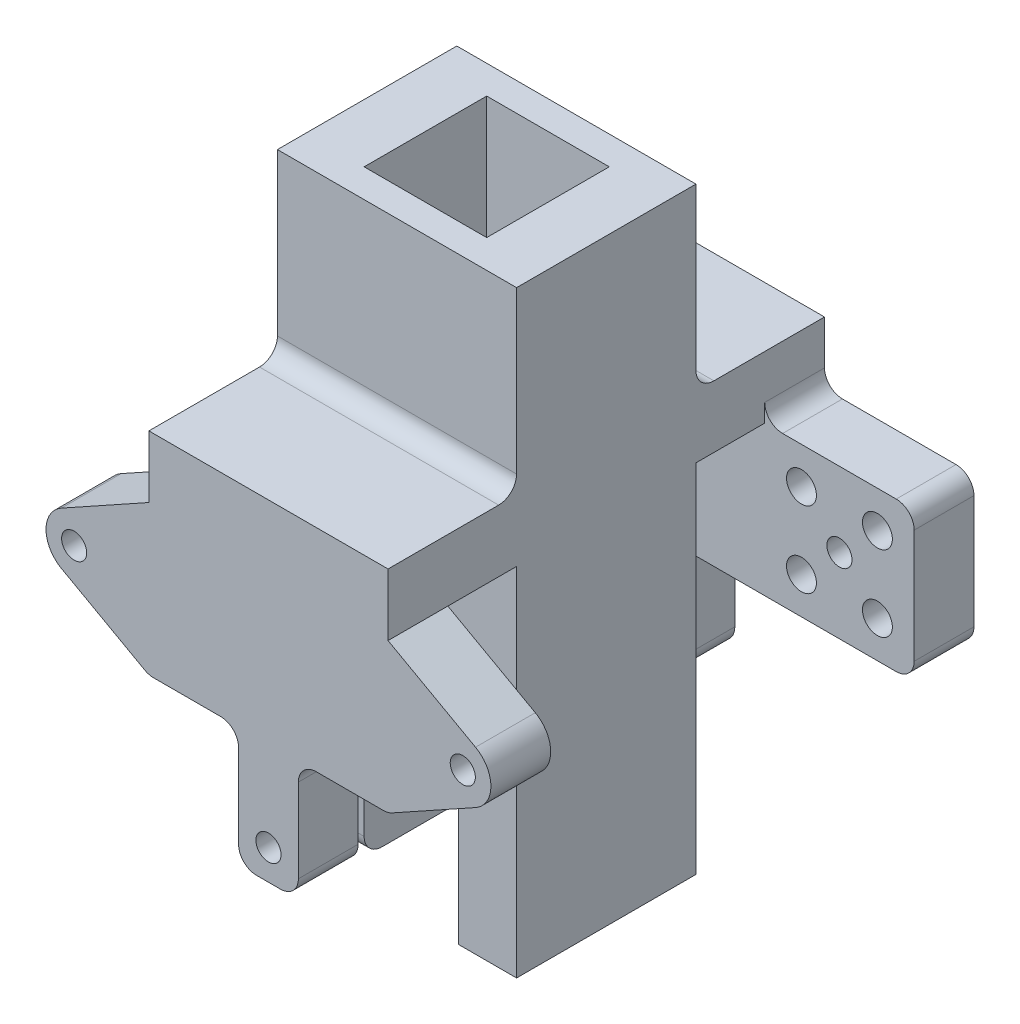
SolidWorks part; units mm, degrees
ref_plane "Front Plane" through (0, 0, 0) normal (0, 0, 1) x (1, 0, 0)
ref_plane "Top Plane" through (0, 0, 0) normal (0, 1, 0) x (1, 0, 0)
ref_plane "Right Plane" through (0, 0, 0) normal (1, 0, 0) x (0, 0, -1)
sketch "Sketch2" plane through (0, 0, 0) normal (0, 1, 0) x (1, 0, 0)
  line L14 (-20, 15) -> (20, 15)
  line L15 (-20, 15) -> (-20, -15)
  line L16 (-20, -15) -> (20, -15)
  line L17 (20, 15) -> (20, -15)
  line L18 (-20, 15) -> (20, -15) construction
  line L19 (-20, -15) -> (20, 15) construction
  point P0 (0, 0)
  dimension "D1" = 40
  dimension "D2" = 30
extrude "Boss-Extrude1" add sketch "Sketch2" along normal blind 100
sketch "Sketch3" plane through (0, 0, 0) normal (0, 1, 0) x (1, 0, 0)
  line L1 (-10.25, 10.25) -> (10.25, 10.25)
  line L2 (-10.25, 10.25) -> (-10.25, -10.25)
  line L3 (-10.25, -10.25) -> (10.25, -10.25)
  line L4 (10.25, 10.25) -> (10.25, -10.25)
  line L5 (-10.25, 10.25) -> (10.25, -10.25) construction
  line L6 (-10.25, -10.25) -> (10.25, 10.25) construction
  point P0 (0, 0)
  dimension "D1" = 20.5
  dimension "D2" = 20.5
extrude "Cut-Extrude1" cut sketch "Sketch3" along normal blind 100
sketch "Sketch4" plane through (0, 0, 15) normal (0, 0, 1) x (1, 0, 0)
  line L1 (-10.25, -25) -> (10.25, -25)
  line L2 (-10.25, -25) -> (-10.25, 25)
  line L3 (-10.25, 25) -> (10.25, 25)
  line L4 (10.25, -25) -> (10.25, 25)
  line L5 (-10.25, -25) -> (10.25, 25) construction
  line L6 (-10.25, 25) -> (10.25, -25) construction
  point P0 (0, 0)
  dimension "D1" = 20.5
  dimension "D2" = 50
extrude "Cut-Extrude2" cut sketch "Sketch4" against normal up to surface (4.75 mm away) up to face at (0, 50, 10.25)
sketch "Sketch5" plane through (-10.25, 0, 0) normal (1, 0, 0) x (0, 0, -1)
  line L1 (-10.25, 25) -> (-15, 25)
  line L2 (-10.25, 25) -> (-10.25, 0)
  line L3 (-10.25, 0) -> (-15, 0)
  line L4 (-15, 25) -> (-15, 0)
extrude "Cut-Extrude4" cut sketch "Sketch5" against normal up to surface (9.75 mm away) up to face at (-20, 50, 0)
sketch "Sketch6" plane through (-20, 0, 0) normal (-1, 0, 0) x (0, 0, 1)
  line L0 (10.25, 12.5) -> (-15, 12.5) construction
  line L1 (10.25, 25) -> (10.25, 0) construction
  line L2 (-15, 100) -> (-15, 0) construction
  line L4 (10.25, 12.5) -> (15.125, 12.5) construction
  line L5 (-3.925, 12.5) -> (-3.925, 18.85) construction
  circle A0 centre (2.425, 12.5) radius 2.1
  circle A1 centre (-10.275, 12.5) radius 2.1
  circle A2 centre (-3.925, 18.85) radius 2.1
  circle A3 centre (-3.925, 6.15) radius 2.1
  dimension "D2" = 12.7
  dimension "D3" = 4.2
  dimension "D4" = 12.7
  dimension "D5" = 4.2
  dimension "D7" = 6.35
  dimension "D1" = 4.875
  dimension "D6" = 6.35
extrude "Cut-Extrude5" cut sketch "Sketch6" against normal up to surface (9.75 mm away) up to face at (-10.25, 45, 2.05)
sketch "Sketch7" plane through (-10.25, 0, 0) normal (1, 0, 0) x (0, 0, -1)
  circle A0 centre (-2.425, 12.5) radius 2.5
  circle A1 centre (10.275, 12.5) radius 2.5
  circle A2 centre (3.925, 18.85) radius 2.5
  circle A6 centre (3.925, 6.15) radius 2.5
  dimension "D1" = 12.7
extrude "Cut-Extrude6" cut sketch "Sketch7" against normal blind 5.18
sketch "Sketch8" plane through (0, 0, -15) normal (0, 0, -1) x (-1, 0, 0)
  line L0 (-20, 100) -> (-20, 0) construction
  line L1 (20, 100) -> (20, 0) construction
  line L2 (-20, 59.62) -> (20, 59.62)
  line L3 (-20, 59.62) -> (-20, 70)
  line L4 (-20, 70) -> (20, 70)
  line L5 (20, 59.62) -> (20, 70)
  line L6 (-20, 0) -> (20, 0) construction
  dimension "D1" = 59.62
  dimension "D2" = 10.38
extrude "Boss-Extrude2" add sketch "Sketch8" along normal blind 21.5
sketch "Sketch9" plane through (0, 59.62, 0) normal (0, -1, 0) x (1, 0, 0)
  line L0 (20, -36.5) -> (20, -15) construction
  line L1 (-20, -36.5) -> (20, -36.5)
  line L2 (-20, -36.5) -> (-20, -26.5)
  line L3 (-20, -26.5) -> (20, -26.5)
  line L4 (20, -36.5) -> (20, -26.5)
  dimension "D1" = 10
extrude "Boss-Extrude3" add sketch "Sketch9" along normal blind 45
sketch "Sketch10" plane through (0, 0, -36.5) normal (0, 0, -1) x (-1, 0, 0)
  line L0 (-20, 47.125) -> (20, 47.125) construction
  line L1 (-20, 70) -> (-20, 14.62) construction
  line L2 (20, 14.62) -> (20, 70) construction
  line L3 (20, 70) -> (-20, 70) construction
  dimension "D1" = 22.875
sketch "Sketch11" plane through (20, 0, 0) normal (1, 0, 0) x (0, 0, -1)
  line L5 (36.5, 47.125) -> (25.5, 47.125) construction
  line L6 (26.5, 14.62) -> (26.5, 59.62) construction
  line L7 (36.5, 70) -> (36.5, 14.62) construction
  line L8 (26.5, 59.625) -> (36.5, 59.625)
  line L9 (26.5, 59.625) -> (26.5, 34.625)
  line L10 (26.5, 34.625) -> (36.5, 34.625)
  line L11 (36.5, 59.625) -> (36.5, 34.625)
  dimension "D1" = 25
extrude "Boss-Extrude4" add sketch "Sketch11" along normal blind 25 and the other way offset from surface (65 mm away) 25 other way up to face at (-20, 12.5, 4.525)
sketch "Sketch13" plane through (0, 0, -36.5) normal (0, 0, -1) x (-1, 0, 0)
  line L0 (-45, 34.625) -> (-20, 59.625) construction
  line L1 (-20, 34.625) -> (-45, 59.625) construction
  circle A0 centre (-32.5, 47.125) radius 2.1
  circle A1 centre (-26.15, 53.475) radius 2.1
  circle A2 centre (-38.85, 53.475) radius 2.1
  circle A3 centre (-38.85, 40.775) radius 2.1
  circle A4 centre (-26.15, 40.775) radius 2.1
  dimension "D1" = 12.7
  dimension "D2" = 6.35
  dimension "D3" = 12.7
  dimension "D4" = 6.35
extrude "Cut-Extrude7" cut sketch "Sketch13" against normal blind 4.57
sketch "Sketch14" plane through (0, 0, -26.5) normal (0, 0, 1) x (1, 0, 0)
  circle A0 centre (32.5, 47.125) radius 2.1
  circle A1 centre (38.85, 53.475) radius 2.5
  circle A2 centre (26.15, 53.475) radius 2.5
  circle A3 centre (26.15, 40.775) radius 2.5
  circle A4 centre (38.85, 40.775) radius 2.5
extrude "Cut-Extrude8" cut sketch "Sketch14" against normal up to surface (5.43 mm away) up to face at (36.75, 53.475, -31.93)
sketch "Sketch15" plane through (0, 0, -36.5) normal (0, 0, -1) x (-1, 0, 0)
  line L0 (20, 34.625) -> (45, 59.625) construction
  line L1 (45, 34.625) -> (20, 59.625) construction
  line L2 (20, 59.625) -> (34.6326, 51.4958)
  line L3 (34.6326, 42.7542) -> (20, 34.625)
  line L4 (20, 34.625) -> (45, 34.625)
  line L5 (45, 34.625) -> (45, 59.625)
  line L6 (45, 59.625) -> (20, 59.625)
  line L7 (-20, 47.125) -> (20, 47.125) construction
  circle A0 centre (32.5, 47.125) radius 2.1
  arc A1 (34.6326, 42.7542) -> (34.6326, 51.4958) centre (32.2044, 47.125) ccw
  circle A2 centre (0, 19.65) radius 2.1
  point P13 (42.5, 47.125)
  dimension "D1" = 10
  dimension "D2" = 5
  dimension "D3" = 27.475
extrude "Cut-Extrude9" cut sketch "Sketch15" against normal up to surface (10 mm away) up to face at (41.35, 40.775, -26.5)
mirror "Mirror2" about plane through (0, 0, 0) normal (0, 0, 1) of "Cut-Extrude9", "Boss-Extrude2", "Boss-Extrude3", "Boss-Extrude4"
sketch "Sketch18" plane through (0, 0, 36.5) normal (0, 0, 1) x (1, 0, 0)
  line L0 (20, 34.625) -> (45, 34.625) construction
  line L1 (20, 59.625) -> (34.6326, 51.4958)
  line L2 (34.6326, 42.7542) -> (20, 34.625)
  line L3 (20, 34.625) -> (45, 34.625)
  line L4 (45, 34.625) -> (45, 59.625)
  line L5 (45, 59.625) -> (20, 59.625)
  line L6 (-20, 34.625) -> (20, 34.625) construction
  circle A0 centre (32.5, 47.125) radius 2.1
  arc A1 (34.6326, 51.4958) -> (34.6326, 42.7542) centre (32.2044, 47.125) cw
  point P16 (42.5, 47.125)
  point P25 (0, 19.65)
  line M12 (20, 34.625) -> (45, 34.625)
  line M13 (45, 34.625) -> (45, 59.625)
  line M14 (45, 59.625) -> (20, 59.625)
  dimension "D1" = 12.5
  dimension "D4" = 5
  dimension "D2" = 12.5
  dimension "D3" = 10
extrude "Cut-Extrude10" cut sketch "Sketch18" against normal up to surface (10 mm away) contours L1 A1 L2 M12 M13 M14 | A0
sketch "Sketch19" plane through (0, 0, 36.5) normal (0, 0, 1) x (1, 0, 0)
  line L0 (-20, 34.625) -> (20, 34.625) construction
  line L1 (-20, 14.62) -> (20, 14.62) construction
  line L2 (-5, 34.625) -> (5, 34.625)
  line L3 (-5, 34.625) -> (-5, 14.62)
  line L4 (-5, 14.62) -> (5, 14.62)
  line L5 (5, 34.625) -> (5, 14.62)
  circle A0 centre (0, 19.65) radius 2.1 construction
  line M4 (20, 14.62) -> (20, 34.625)
  line M14 (-20, 34.625) -> (-20, 14.62)
  line M15 (-20, 14.62) -> (20, 14.62)
  dimension "D2" = 5
  dimension "D1" = 10
extrude "Cut-Extrude11" cut sketch "Sketch19" along a picked direction on the side against the normal blind 12.57 contours L0 L3 M14 M15 | L0 L5 M15 M4
mirror "Mirror3" about plane through (0, 0, 0) normal (0, 0, 1) of "Cut-Extrude11"
fillet "Fillet1" radius 3 17 edges at (0, 70, -15) (20, 59.625, -31.5) (-20, 34.625, -31.5) (45, 34.625, -31.5) (45, 59.625, -31.5) (0, 70, 15) (20, 34.625, 31.5) (-20, 34.625, 31.5) (5, 14.62, 31.5) (-5, 14.62, 31.5) (-5, 34.625, 31.5) (5, 34.625, 31.5) (5, 14.62, -31.5) (-5, 14.62, -31.5) (-5, 34.625, -31.5) (5, 34.625, -31.5) (-15.125, 0, 10.25)
